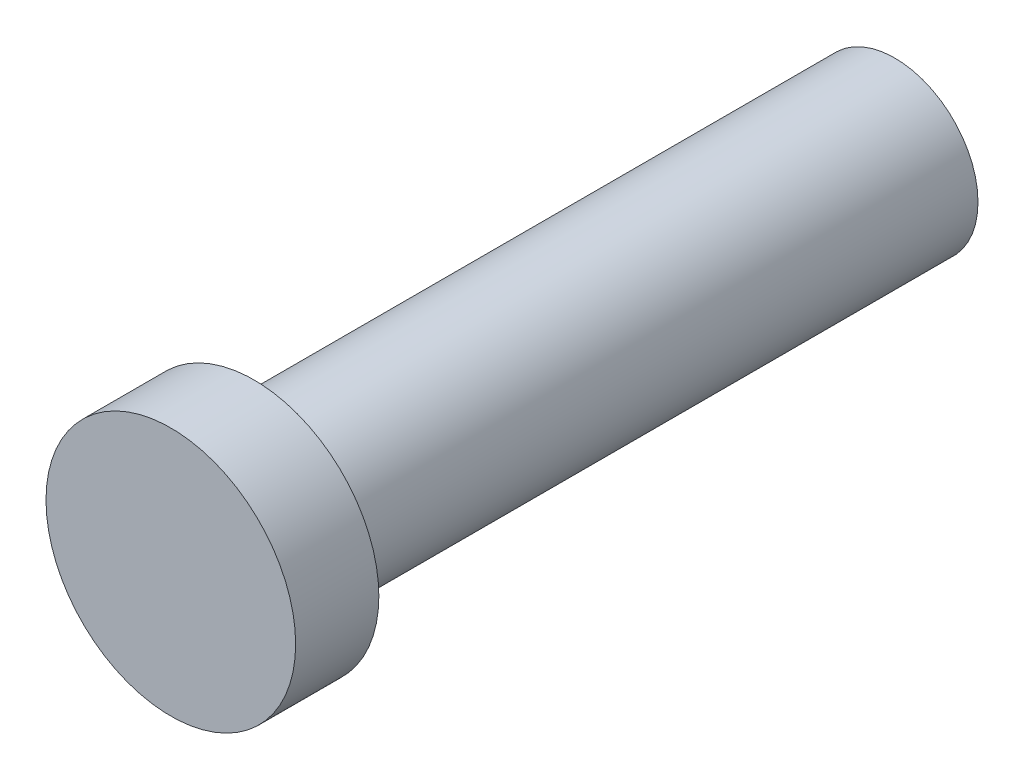
SolidWorks part; units mm, degrees
ref_plane "Front Plane" through (0, 0, 0) normal (0, 0, 1) x (1, 0, 0)
ref_plane "Top Plane" through (0, 0, 0) normal (0, 1, 0) x (1, 0, 0)
ref_plane "Right Plane" through (0, 0, 0) normal (1, 0, 0) x (0, 0, -1)
sketch "Sketch1" plane through (0, 0, 0) normal (0, 0, 1) x (1, 0, 0)
  circle A0 centre (0, 0) radius 1
  dimension "D1" = 2
extrude "Boss-Extrude1" add sketch "Sketch1" along normal blind 7.7
sketch "Sketch2" plane through (0, 0, 7.7) normal (0, 0, 1) x (1, 0, 0)
  circle A0 centre (0, 0) radius 1.5
  dimension "D1" = 3
extrude "Boss-Extrude2" add sketch "Sketch2" along normal blind 1
